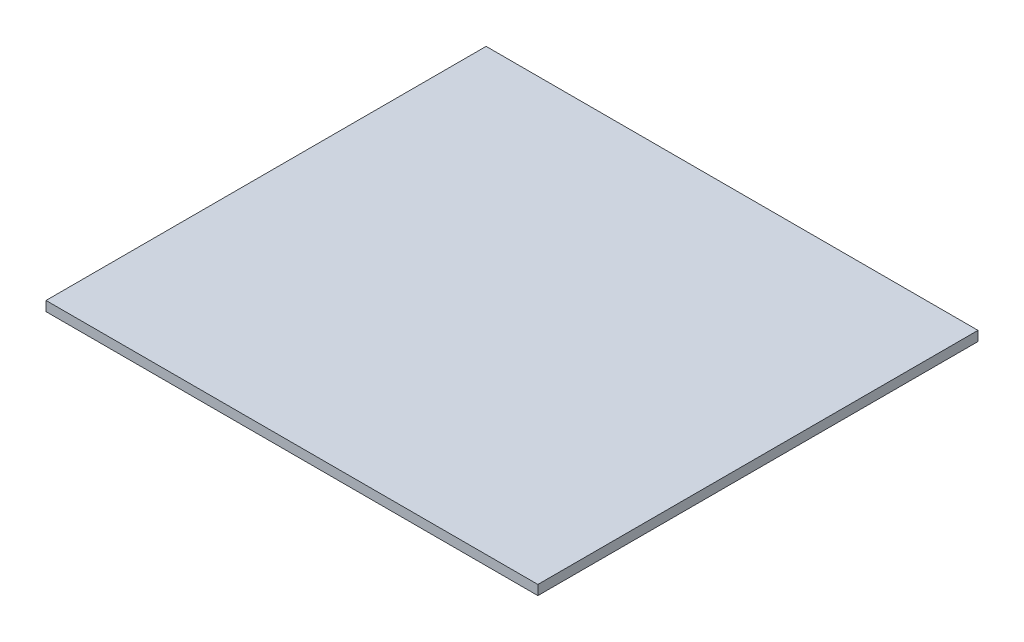
SolidWorks part; units mm, degrees
ref_plane "Front" through (0, 0, 0) normal (0, 0, 1) x (1, 0, 0)
ref_plane "Top" through (0, 0, 0) normal (0, 1, 0) x (1, 0, 0)
ref_plane "Right" through (0, 0, 0) normal (1, 0, 0) x (0, 0, -1)
sketch "Sketch1" plane through (0, 0, 0) normal (0, 1, 0) x (1, 0, 0)
  line L1 (0, 0) -> (304, 0)
  line L2 (0, 0) -> (0, 272)
  line L3 (0, 272) -> (304, 272)
  line L4 (304, 0) -> (304, 272)
  dimension "D1" = 304
  dimension "D2" = 272
extrude "Boss-Extrude1" add sketch "Sketch1" along normal blind 6
